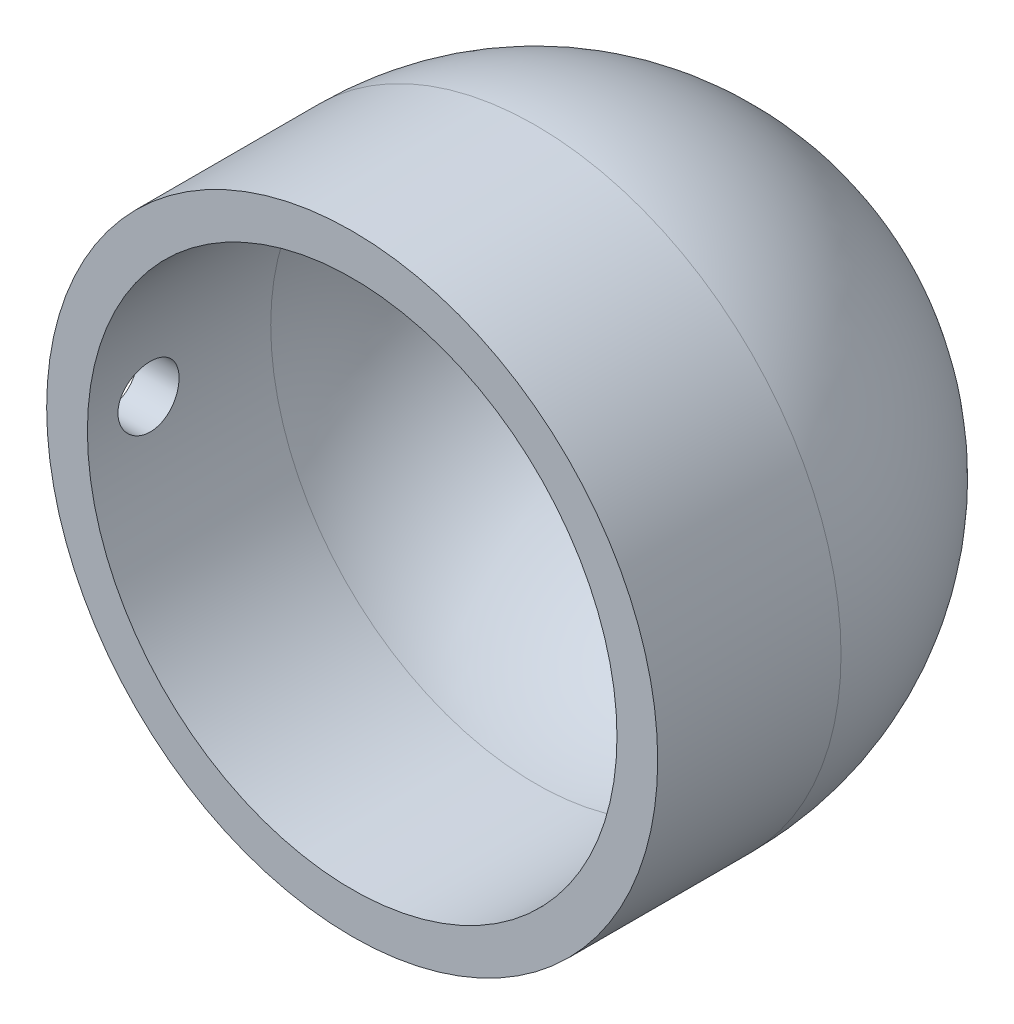
SolidWorks part; units mm, degrees
ref_plane "Front Plane" through (0, 0, 0) normal (0, 0, 1) x (1, 0, 0)
ref_plane "Top Plane" through (0, 0, 0) normal (0, 1, 0) x (1, 0, 0)
ref_plane "Right Plane" through (0, 0, 0) normal (1, 0, 0) x (0, 0, -1)
sketch "Sketch2" plane through (0, 0, 0) normal (0, 1, 0) x (1, 0, 0)
  line L19 (0, 0) -> (0, -9)
  line L20 (0, -9) -> (2, -9)
  line L30 (28, -8.3222) -> (28, -9)
  line L31 (28, -9) -> (30, -9)
  line L32 (2, -7) -> (28, -7) construction
  line L33 (0, -9) -> (30, -9) construction
  line L34 (2, 0) -> (2, -7) construction
  line L35 (28, 0) -> (28, -7) construction
  line L36 (2, 0) -> (2, -9)
  line L37 (28, 0) -> (28, -9)
  line L38 (15, 26.392) -> (15, -5.1789) construction
  line L39 (31.2383, -7.5) -> (-1.9776, -7.5) construction
  line L40 (30, 0) -> (30, -9) construction
  line L41 (30, 0) -> (30, -9)
  line L43 (15, 15) -> (15, 13)
  line L44 (0, -6) -> (2, -6)
  line L46 (34.9987, -7.7947) -> (34.8093, -7.7947)
  line L47 (34.9987, -7.7947) -> (34.9987, -6.81)
  line L48 (34.9987, -6.81) -> (34.8093, -6.81)
  line L49 (34.8093, -7.7947) -> (34.8093, -6.81)
  arc A2 (0, 0) -> (30, 0) centre (15, 0) cw
  arc A3 (2, 0) -> (28, 0) centre (15, 0) cw
  point P21 (15, 13)
  dimension "D1" = 2
  dimension "D2" = 22
  dimension "D3" = 3
  dimension "D4" = 1.5
  dimension "D5" = 26
revolve "Revolve3" add sketch "Sketch2" angle 360 about L38
sketch "Sketch4" plane through (0, 0, 0) normal (1, 0, 0) x (0, 0, -1)
  line L0 (-9, 0) -> (-9, 13.7954) construction
  line L1 (-9, 0) -> (-4.2824, 0) construction
  line L2 (13.2, 0) -> (-13.2, 0) construction
  line L3 (-6, 0) -> (-6, 5.4849) construction
  line L4 (-9, 15) -> (-9, -15) construction
  circle A0 centre (-6, 0) radius 1.5
  point P10 (0, 0)
  dimension "D1" = 3
  dimension "D2" = 0
extrude "Cut-Extrude1" cut sketch "Sketch4" along normal blind 10 contours A0
